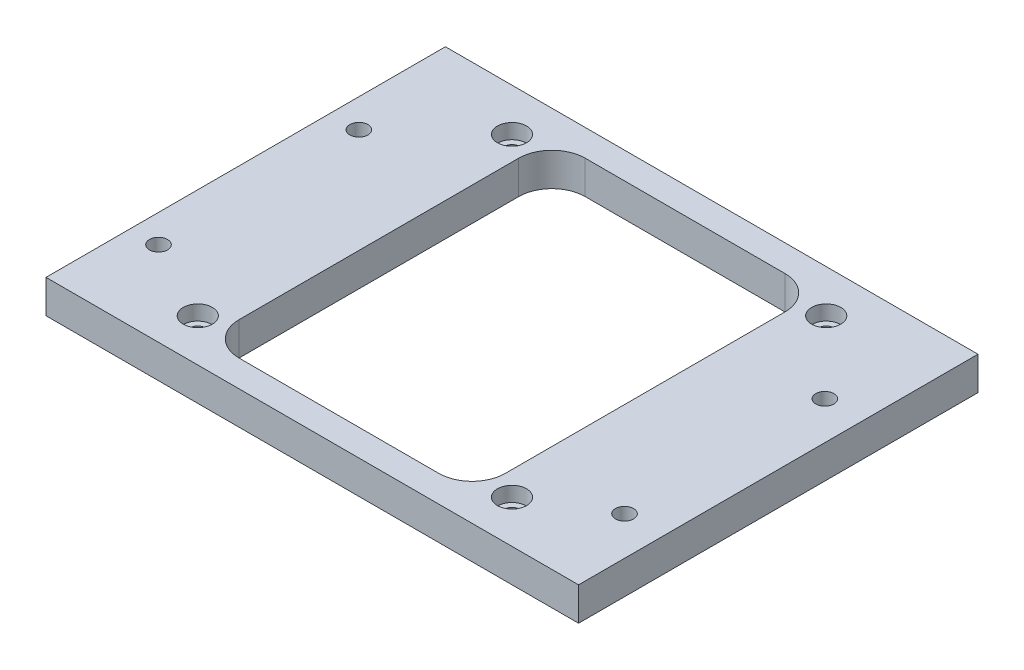
SolidWorks part; units mm, degrees
material "6061 Alloy"
ref_plane "Front Plane" through (0, 0, 0) normal (0, 0, 1) x (1, 0, 0)
ref_plane "Top Plane" through (0, 0, 0) normal (0, 1, 0) x (1, 0, 0)
ref_plane "Right Plane" through (0, 0, 0) normal (1, 0, 0) x (0, 0, -1)
sketch "Sketch2" plane through (0, 0, 0) normal (0, 1, 0) x (1, 0, 0)
  line L1 (-50.8, 38.1) -> (50.8, 38.1)
  line L2 (-50.8, 38.1) -> (-50.8, -38.1)
  line L3 (-50.8, -38.1) -> (50.8, -38.1)
  line L4 (50.8, 38.1) -> (50.8, -38.1)
  line L5 (-19.05, 33.02) -> (19.05, 33.02)
  line L6 (-25.4, 26.67) -> (-25.4, -26.67)
  line L7 (-19.05, -33.02) -> (19.05, -33.02)
  line L8 (25.4, 26.67) -> (25.4, -26.67)
  arc A0 (19.05, -33.02) -> (25.4, -26.67) centre (19.05, -26.67) ccw
  arc A1 (-19.05, -33.02) -> (-25.4, -26.67) centre (-19.05, -26.67) cw
  arc A2 (19.05, 33.02) -> (25.4, 26.67) centre (19.05, 26.67) cw
  arc A3 (-19.05, 33.02) -> (-25.4, 26.67) centre (-19.05, 26.67) ccw
  point P10 (25.4, -33.02)
  point P13 (-25.4, -33.02)
  point P16 (25.4, 33.02)
  dimension "D7" = 6.35
  dimension "D1" = 101.6
  dimension "D2" = 76.2
  dimension "D3" = 50.8
  dimension "D4" = 66.04
  dimension "D5" = 33.02
  dimension "D6" = 25.4
  dimension "D8" = 50.8
  dimension "D9" = 38.1
extrude "Boss-Extrude1" add sketch "Sketch2" along normal blind 6.35
hole_wizard "CBORE for #4 Socket Head Cap Screw1" positions "Sketch5" profile "Sketch4" counterbore size "#4" standard "ANSI Inch" end condition through all
sketch "Sketch5" plane through (0, 6.35, 0) normal (0, 1, 0) x (1, 0, 0)
  point P0 (-29.972, 29.972)
  point P2 (29.972, 29.972)
  point P4 (29.972, -29.972)
  point P6 (-29.972, -29.972)
  dimension "D1" = 29.972
  dimension "D2" = 29.972
  dimension "D3" = 59.944
  dimension "D4" = 59.944
  dimension "D5" = 59.944
  dimension "D6" = 59.944
sketch "Sketch4" plane through (-29.972, 6.35, -29.972) normal (1, 0, 0) x (0, 0, 1)
  line L0 (0, 0) -> (0, 6.35)
  line L1 (0, 6.35) -> (1.6319, 6.35)
  line L3 (1.6319, 6.35) -> (1.632, 2.8448)
  line L4 (1.632, 2.8448) -> (2.7788, 2.8448)
  line L5 (2.7788, 2.8448) -> (2.7788, 0)
  line L7 (2.7788, 0) -> (0, 0)
  line L11 (0, -6.35) -> (0, 107.95) construction
  dimension "Thru Hole Dia." = 3.2639
  dimension "Thru Hole Depth" = 6.35
  dimension "C'Bore Dia." = 5.5575
  dimension "C'Bore Depth" = 2.8448
hole_wizard "#8-32 Tapped Hole1" positions "Sketch7" profile "Sketch6" tap size "#8-32" standard "ANSI Inch" end condition through all
sketch "Sketch7" plane through (0, 6.35, 0) normal (0, 1, 0) x (1, 0, 0)
  point P0 (-45.339, 16.129)
  point P2 (-45.466, -21.971)
  point P4 (43.561, 16.129)
  point P6 (43.434, -21.971)
  dimension "D1" = 38.1
  dimension "D2" = 45.339
  dimension "D3" = 38.1
  dimension "D4" = 16.129
  dimension "D5" = 88.9
  dimension "D6" = 88.9
  dimension "D7" = 45.466
  dimension "D8" = 43.434
sketch "Sketch6" plane through (-45.339, 6.35, -16.129) normal (1, 0, 0) x (0, 0, 1)
  line L0 (0, 0) -> (0, 6.35)
  line L1 (0, 6.35) -> (1.7272, 6.35)
  line L2 (1.7272, 6.35) -> (1.7272, 0)
  line L5 (1.7272, 0) -> (0, 0)
  line L11 (0, -6.35) -> (0, 107.95) construction
  dimension "Thru Tap Drill Dia." = 3.4544
  dimension "Thru Tap Drill Depth" = 6.35
cosmetic thread "Hole Thread1" parameters "D2"=4.1656
cosmetic thread "Hole Thread2" parameters "D2"=4.1656
cosmetic thread "Hole Thread3" parameters "D2"=4.1656
cosmetic thread "Hole Thread4" parameters "D2"=4.1656
